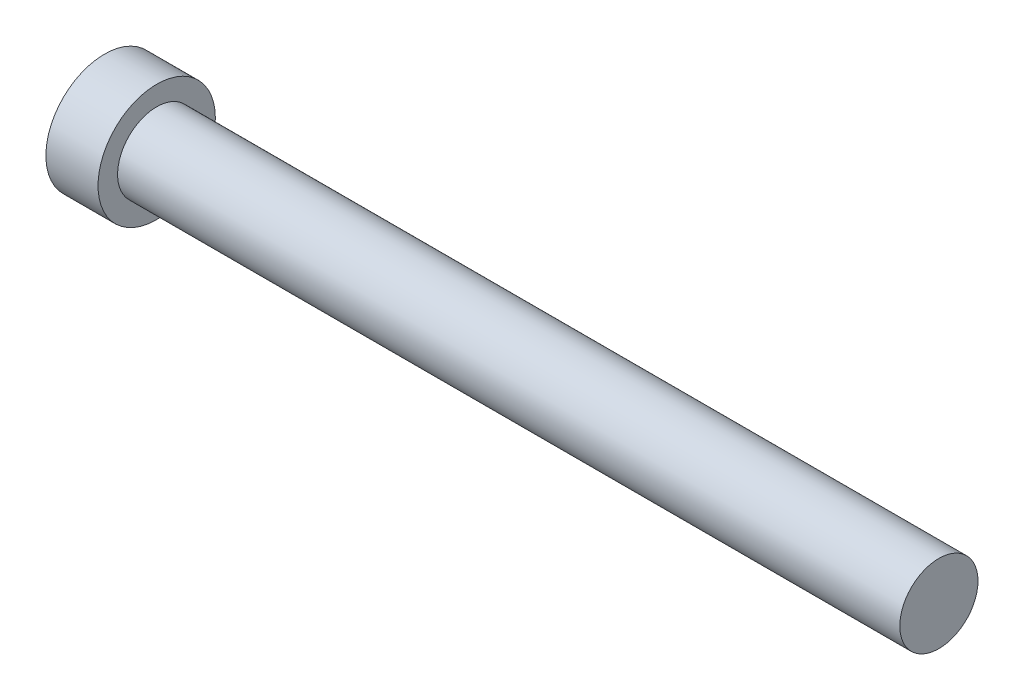
SolidWorks part; units mm, degrees
ref_plane "Front Plane" through (0, 0, 0) normal (0, 0, 1) x (1, 0, 0)
ref_plane "Top Plane" through (0, 0, 0) normal (0, 1, 0) x (1, 0, 0)
ref_plane "Right Plane" through (0, 0, 0) normal (1, 0, 0) x (0, 0, -1)
sketch "Sketch1" plane through (0, 0, 0) normal (1, 0, 0) x (0, 0, -1)
  circle A0 centre (0, 0) radius 2.25
  dimension "D1" = 4.5
extrude "Boss-Extrude1" add sketch "Sketch1" along normal blind 2
sketch "Sketch2" plane through (2, 0, 0) normal (1, 0, 0) x (0, 0, -1)
  circle A0 centre (0, 0) radius 1.5
  dimension "D1" = 3
extrude "Boss-Extrude2" add sketch "Sketch2" along normal blind 30
